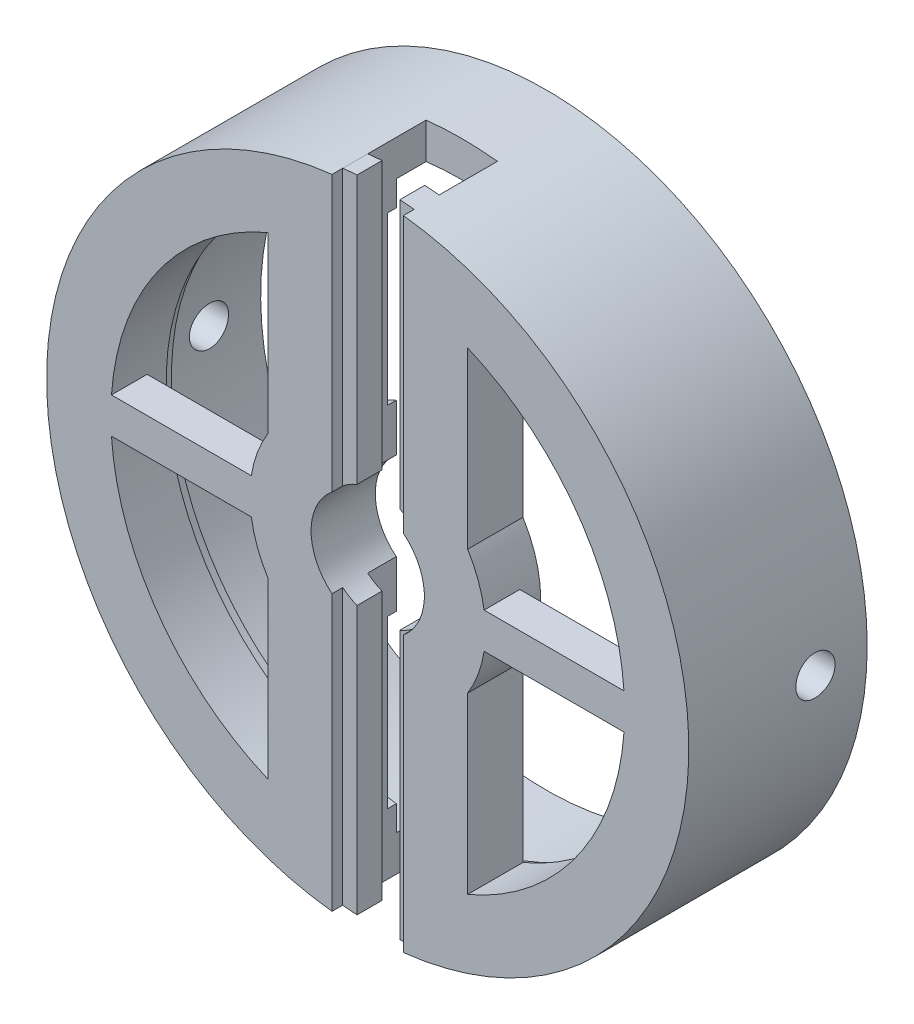
SolidWorks part; units mm, degrees
ref_plane "Front Plane" through (0, 0, 0) normal (0, 0, 1) x (1, 0, 0)
ref_plane "Top Plane" through (0, 0, 0) normal (0, 1, 0) x (1, 0, 0)
ref_plane "Right Plane" through (0, 0, 0) normal (1, 0, 0) x (0, 0, -1)
sketch "Sketch1" plane through (0, 0, 0) normal (-1, 0, 0) x (0, 0, 1)
  line L0 (0, 0) -> (0, 80) construction
  line L1 (0, 80) -> (45, 80)
  line L2 (47.5, 73) -> (47.5, 27.5)
  line L3 (45, 15) -> (63, 15)
  line L4 (63, 15) -> (63, 90)
  line L5 (63, 90) -> (0, 90)
  line L6 (0, 90) -> (0, 80)
  line L7 (0, 0) -> (63, 0) construction
  line L11 (45, 15) -> (45, 27.5)
  line L12 (45, 27.5) -> (47.5, 27.5)
  line L13 (47.5, 73) -> (45, 73)
  line L14 (45, 73) -> (45, 80)
  line L16 (42.7868, 58.5) -> (10, 58.5) construction
  line L17 (10, 58.5) -> (10, 15) construction
  line L18 (10, 15) -> (42.7868, 15) construction
  line L19 (15, 90) -> (15, 80) construction
  line L20 (40, 90) -> (40, 80) construction
  line L21 (40, 85) -> (15, 85) construction
  line L22 (27.5, 85) -> (27.5, 58.5) construction
  point P27 (27.5, 85)
  point P30 (27.5, 58.5)
  dimension "D1" = 180
  dimension "D2" = 30
  dimension "D3" = 63
  dimension "D4" = 15.5
  dimension "D5" = 160
  dimension "D7" = 2.5
  dimension "D9" = 146
  dimension "D10" = 55
  dimension "D12" = 58.5
  dimension "D13" = 5
  dimension "D14" = 35.5
  dimension "D15" = 25
sketch "Sketch2" plane through (0, 0, 0) normal (0, 1, 0) x (1, 0, 0)
  line L0 (10, -53) -> (10, -45)
  line L1 (10, -53) -> (6, -53)
  line L2 (-10, -63) -> (10, -63)
  line L3 (-10, -60) -> (-10, -63)
  line L4 (-10, -60) -> (-6, -60)
  line L5 (-6, -53) -> (-6, -60)
  line L6 (-6, -53) -> (-10, -53)
  line L7 (-10, -53) -> (-10, -45)
  line L8 (-10, -45) -> (10, -45)
  line L9 (10, -60) -> (10, -63)
  line L10 (6, -60) -> (10, -60)
  line L11 (6, -53) -> (6, -60)
  line L12 (0, -63) -> (0, -45) construction
  line L13 (0, 0) -> (0, -45) construction
  circle A0 centre (0, -27.5) radius 12.5 construction
  dimension "D3" = 25
  dimension "D1" = 20
  dimension "D2" = 8
  dimension "D4" = 3
  dimension "D5" = 12
sketch "Sketch3" plane through (0, 0, 0) normal (1, 0, 0) x (0, 0, -1)
  line L6 (-45, 80) -> (0, 80)
  line L7 (-47.5, 27.5) -> (-47.5, 73)
  line L8 (-63, 15) -> (-45, 15)
  line L9 (-63, 90) -> (-63, 15)
  line L10 (0, 90) -> (-63, 90)
  line L11 (0, 80) -> (0, 90)
  line L12 (-45, 80) -> (0, 80)
  line L13 (-47.5, 27.5) -> (-47.5, 73)
  line L14 (-63, 15) -> (-45, 15)
  line L15 (-63, 90) -> (-63, 15)
  line L16 (0, 90) -> (-63, 90)
  line L17 (0, 80) -> (0, 90)
  line L25 (-45, 73) -> (-45, 80)
  line L26 (-45, 73) -> (-45, 80)
  line L27 (-47.5, 73) -> (-45, 73)
  line L28 (-47.5, 73) -> (-45, 73)
  line L29 (-45, 27.5) -> (-47.5, 27.5)
  line L30 (-45, 27.5) -> (-47.5, 27.5)
  line L31 (-45, 15) -> (-45, 27.5)
  line L32 (-45, 15) -> (-45, 27.5)
  dimension "D1" = 0
revolve "Revolve2" add sketch "Sketch3" angle 360 about L7
sketch "Sketch4" plane through (0, 0, 0) normal (0, 1, 0) x (1, 0, 0)
  line L12 (10, -53) -> (10, -45)
  line L13 (10, -45) -> (-10, -45)
  line L14 (-10, -45) -> (-10, -53)
  line L15 (-10, -53) -> (-6, -53)
  line L16 (-6, -53) -> (-6, -60)
  line L17 (-6, -60) -> (-10, -60)
  line L18 (-10, -60) -> (-10, -63)
  line L19 (-10, -63) -> (10, -63)
  line L20 (10, -63) -> (10, -60)
  line L21 (10, -60) -> (6, -60)
  line L22 (6, -60) -> (6, -53)
  line L23 (6, -53) -> (10, -53)
  line L24 (10, -53) -> (10, -45)
  line L25 (10, -45) -> (-10, -45)
  line L26 (-10, -45) -> (-10, -53)
  line L27 (-10, -53) -> (-6, -53)
  line L28 (-6, -53) -> (-6, -60)
  line L29 (-6, -60) -> (-10, -60)
  line L30 (-10, -60) -> (-10, -63)
  line L31 (-10, -63) -> (10, -63)
  line L32 (10, -63) -> (10, -60)
  line L33 (10, -60) -> (6, -60)
  line L34 (6, -60) -> (6, -53)
  line L35 (6, -53) -> (10, -53)
  dimension "D1" = 0
extrude "Cut-Extrude1" cut sketch "Sketch4" along normal through all
sketch "Sketch35" plane through (0, 0, 0) normal (0, 1, 0) x (1, 0, 0)
  line L0 (-10, -45) -> (-10, -36.65)
  line L1 (-10, -36.65) -> (10, -36.65)
  line L2 (10, -36.65) -> (10, -45)
  line L12 (10, -53) -> (10, -45)
  line L13 (10, -45) -> (-10, -45)
  line L14 (-10, -45) -> (-10, -53)
  line L15 (-10, -53) -> (-6, -53)
  line L16 (-6, -53) -> (-6, -60)
  line L17 (-6, -60) -> (-10, -60)
  line L18 (-10, -60) -> (-10, -63)
  line L19 (-10, -63) -> (10, -63)
  line L20 (10, -63) -> (10, -60)
  line L21 (10, -60) -> (6, -60)
  line L22 (6, -60) -> (6, -53)
  line L23 (6, -53) -> (10, -53)
  line L25 (10, -45) -> (-10, -45)
  dimension "D1" = 0
extrude "Cut-Extrude13" cut sketch "Sketch35" along normal up to next
pattern_circular "CirPattern1" count 2 over 360 about axis through (0, 0, 0) along (0, 0, 1) of "Cut-Extrude1", "Cut-Extrude13"
ref_plane "Plane1" through (0, 0, 100) normal (0, 0, 1) x (1, 0, 0)
ref_plane "Plane7" through (-90, 0, 0) normal (-1, 0, 0) x (0, 0, 1)
sketch "Sketch17" plane through (-90, 0, 0) normal (1, 0, 0) x (0, 0, -1)
  line L0 (0, 0) -> (-63, 0) construction
  circle A0 centre (-27.5, 0) radius 5.5
  dimension "D2" = 11
sketch "Sketch6" plane through (0, 0, 0) normal (0, 1, 0) x (1, 0, 0)
  line L0 (-10, -63) -> (-10, -68)
  line L1 (-10, -68) -> (10, -68)
  line L2 (10, -68) -> (10, -63)
  line L12 (10, -53) -> (10, -45)
  line L13 (10, -45) -> (-10, -45)
  line L14 (-10, -45) -> (-10, -53)
  line L15 (-10, -53) -> (-6, -53)
  line L16 (-6, -53) -> (-6, -60)
  line L17 (-6, -60) -> (-10, -60)
  line L18 (-10, -60) -> (-10, -63)
  line L19 (-10, -63) -> (10, -63)
  line L20 (10, -63) -> (10, -60)
  line L21 (10, -60) -> (6, -60)
  line L22 (6, -60) -> (6, -53)
  line L23 (6, -53) -> (10, -53)
  line L24 (10, -53) -> (10, -45)
  line L25 (10, -45) -> (-10, -45)
  line L26 (-10, -45) -> (-10, -53)
  line L27 (-10, -53) -> (-6, -53)
  line L28 (-6, -53) -> (-6, -60)
  line L29 (-6, -60) -> (-10, -60)
  line L30 (-10, -60) -> (-10, -63)
  line L31 (-10, -63) -> (10, -63) construction
  line L32 (10, -63) -> (10, -60)
  line L33 (10, -60) -> (6, -60)
  line L34 (6, -60) -> (6, -53)
  line L35 (6, -53) -> (10, -53)
  dimension "D2" = 5
  dimension "D1" = 0
sketch "Sketch37" plane through (0, 0, 63) normal (0, 0, 1) x (1, 0, 0)
  line L4 (-28, -66.3325) -> (-28, -17.4642)
  line L5 (-28, 17.4642) -> (-28, 66.3325)
  line L6 (-28, -66.3325) -> (-28, -17.4642)
  line L7 (-28, 17.4642) -> (-28, 66.3325)
  line L10 (28, -17.4642) -> (28, -66.3325)
  line L11 (28, 66.3325) -> (28, 17.4642)
  line L12 (28, -17.4642) -> (28, -66.3325)
  line L13 (28, 66.3325) -> (28, 17.4642)
  arc A4 (-28, 66.3325) -> (-28, -66.3325) centre (0, 0) ccw
  arc A5 (-28, 17.4642) -> (-28, -17.4642) centre (0, 0) ccw
  arc A6 (-28, 66.3325) -> (-28, -66.3325) centre (0, 0) ccw
  arc A7 (-28, 17.4642) -> (-28, -17.4642) centre (0, 0) ccw
  arc A10 (28, -17.4642) -> (28, 17.4642) centre (0, 0) ccw
  arc A11 (28, -66.3325) -> (28, 66.3325) centre (0, 0) ccw
  arc A12 (28, -17.4642) -> (28, 17.4642) centre (0, 0) ccw
  arc A13 (28, -66.3325) -> (28, 66.3325) centre (0, 0) ccw
  dimension "D1" = 18
  dimension "D2" = 18
extrude "Cut-Extrude14" cut sketch "Sketch37" against normal through all
sketch "Sketch38" plane through (0, 0, 0) normal (0, 0, -1) x (-1, 0, 0)
  line L1 (159.2341, 111.0763) -> (-142.6624, 111.0763)
  line L2 (159.2341, 111.0763) -> (159.2341, -121.4364)
  line L3 (159.2341, -121.4364) -> (-142.6624, -121.4364)
  line L4 (-142.6624, 111.0763) -> (-142.6624, -121.4364)
extrude "Cut-Extrude15" cut sketch "Sketch38" against normal blind 13
sketch "Sketch39" plane through (0, 0, 63) normal (0, 0, 1) x (1, 0, 0)
  line L1 (74.1884, -5) -> (20.1778, -5)
  line L2 (74.1884, -5) -> (74.1884, 5)
  line L3 (74.1884, 5) -> (20.1778, 5)
  line L4 (20.1778, -5) -> (20.1778, 5)
  line L5 (-23.4543, -5) -> (-79.5604, -5)
  line L6 (-23.4543, -5) -> (-23.4543, 5)
  line L7 (-23.4543, 5) -> (-79.5604, 5)
  line L8 (-79.5604, -5) -> (-79.5604, 5)
  point P8 (20.1778, 0)
  dimension "D1" = 10
extrude "Boss-Extrude1" add sketch "Sketch39" against normal blind 10
sketch "Sketch41" plane through (0, 0, 63) normal (0, 0, 1) x (1, 0, 0)
  line L0 (18.5565, 105.5049) -> (142.2498, 96.6299)
  line L2 (-18.0066, 103.552) -> (-18.0066, 77.7117)
  line L3 (-18.0066, 77.7117) -> (18.5565, 77.7117)
  line L4 (18.5565, 105.5049) -> (18.5565, 77.7117)
  line L5 (142.2498, 96.6299) -> (80.9247, -147.6442)
  line L6 (80.9247, -147.6442) -> (-121.4009, -133.1273)
  line L7 (-121.4009, -133.1273) -> (-99.9263, 131.7305)
  line L8 (-99.9263, 131.7305) -> (-18.0066, 103.552)
extrude "Cut-Extrude18" cut sketch "Sketch17" against normal through all and the other way through all contours A0
sketch "Sketch42" plane through (0, 0, 63) normal (0, 0, 1) x (1, 0, 0)
  circle A0 centre (0, 0) radius 15.875
  dimension "D1" = 31.75
extrude "Cut-Extrude19" cut sketch "Sketch42" against normal blind 40
